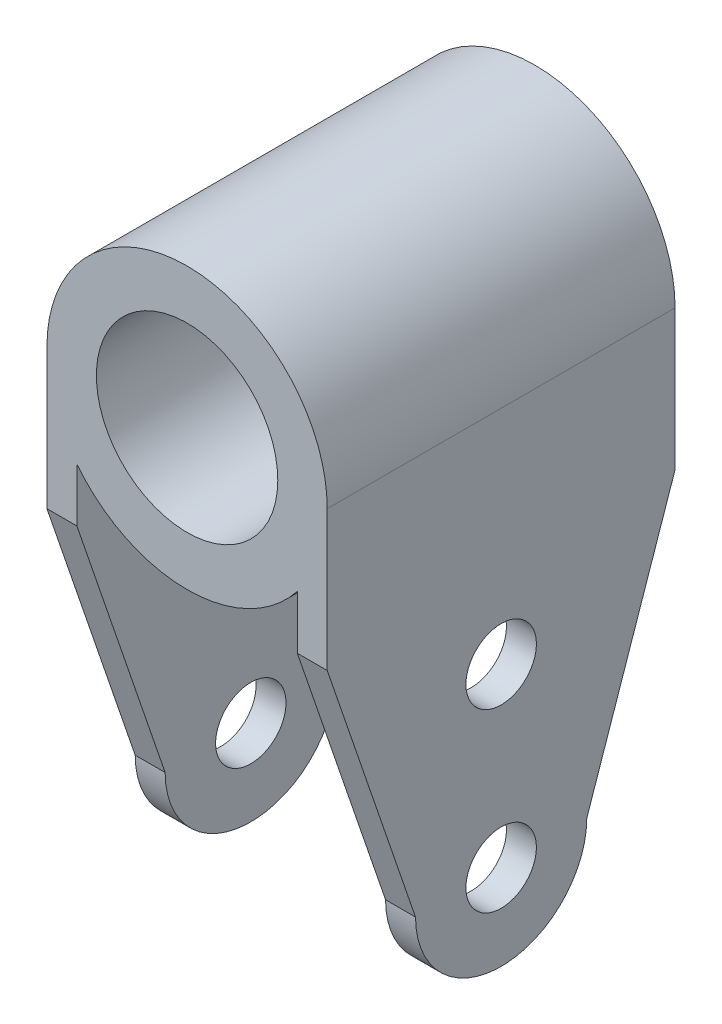
SolidWorks part; units mm, degrees
ref_plane "Front Plane" through (0, 0, 0) normal (0, 0, 1) x (1, 0, 0)
ref_plane "Top Plane" through (0, 0, 0) normal (0, 1, 0) x (1, 0, 0)
ref_plane "Right Plane" through (0, 0, 0) normal (1, 0, 0) x (0, 0, -1)
sketch "Sketch2" plane through (0, 0, 0) normal (0, 0, 1) x (1, 0, 0)
  line L0 (0, -15.915) -> (-22.6713, -15.915) construction
  line L1 (-15.915, 0) -> (-15.915, -15.915)
  line L2 (15.915, 0) -> (15.915, -27.45)
  line L3 (-15.915, -15.915) -> (-15.915, -54.9)
  line L4 (15.915, -27.45) -> (15.915, -54.9)
  line L5 (-15.915, -54.9) -> (-12.515, -54.9)
  line L6 (-12.515, -54.9) -> (-12.515, -9.8317)
  line L7 (15.915, -54.9) -> (12.515, -54.9)
  line L8 (12.515, -54.9) -> (12.515, -9.8317)
  line L9 (0, 15.915) -> (-15.915, 15.915) construction
  line L10 (0, 15.915) -> (15.915, 15.915) construction
  line L11 (0, -10.3) -> (15.915, -10.3) construction
  circle A0 centre (0, 0) radius 10.3
  arc A1 (-12.515, -9.8317) -> (12.515, -9.8317) centre (0, 0) ccw
  circle A2 centre (0, 0) radius 15.915 construction
  arc A3 (15.915, 0) -> (-15.915, 0) centre (0, 0) ccw
  dimension "D1" = 20.6
  dimension "D3" = 44.6
  dimension "D4" = 3.4
  dimension "D5" = 3.4
  dimension "D6" = 25.03
  dimension "D7" = 70.815
  dimension "D2" = 31.83
extrude "Boss-Extrude1" add sketch "Sketch2" along normal blind 39.5
sketch "Sketch3" plane through (-15.915, 0, 0) normal (-1, 0, 0) x (0, 0, 1)
  line L0 (39.5, -9.8317) -> (0, -9.8317) construction
  line L1 (39.5, -9.8317) -> (0, -9.8317) construction
  line L2 (0, -9.8317) -> (10.025, -45.175)
  line L3 (39.5, -54.9) -> (0, -54.9) construction
  line L6 (39.5, -9.8317) -> (29.475, -45.175)
  line L7 (19.75, -9.8317) -> (19.75, -45.175) construction
  line L9 (0, -9.8317) -> (0, -15.915) construction
  line L11 (39.5, -54.9) -> (0, -54.9)
  line L12 (0, -9.8317) -> (0, -15.915)
  line L13 (0, -15.915) -> (10.025, -45.175)
  line L14 (39.5, -15.915) -> (39.5, -9.8317) construction
  line L15 (39.5, -15.915) -> (39.5, -9.8317)
  line L16 (39.5, -15.915) -> (29.475, -45.175)
  circle A2 centre (19.75, -45.175) radius 4.4
  circle A3 centre (19.75, -45.175) radius 9.725
  circle A4 centre (19.75, -25.175) radius 4.4
  line M7 (0, 0) -> (0, -54.9)
  line M8 (0, -54.9) -> (39.5, -54.9)
  line M9 (39.5, -54.9) -> (39.5, 0)
  dimension "D1" = 19.45
  dimension "D2" = 8.8
  dimension "D3" = 20
extrude "Cut-Extrude1" cut sketch "Sketch3" against normal through all contours A3 L2 M7 M8 | A3 L11 L6 M9
hole_wizard "M7 Clearance Hole1" positions "Sketch4" profile "Sketch5" hole size "M7" standard "ANSI Metric" end condition through all
sketch "Sketch4" plane through (-15.915, 0, 0) normal (-1, 0, 0) x (0, 0, 1)
  point P0 (19.75, -45.175)
  point P3 (19.75, -25.175)
sketch "Sketch5" plane through (-15.915, -45.175, 19.75) normal (0, 1, 0) x (0, 0, 1)
  line L0 (0, 0) -> (0, 31.83)
  line L1 (0, 31.83) -> (4, 31.83)
  line L2 (4, 31.83) -> (4, 0)
  line L5 (4, 0) -> (0, 0)
  line L11 (0, -6.35) -> (0, 107.95) construction
  dimension "Thru Hole Dia." = 8
  dimension "Thru Hole Depth" = 31.83
